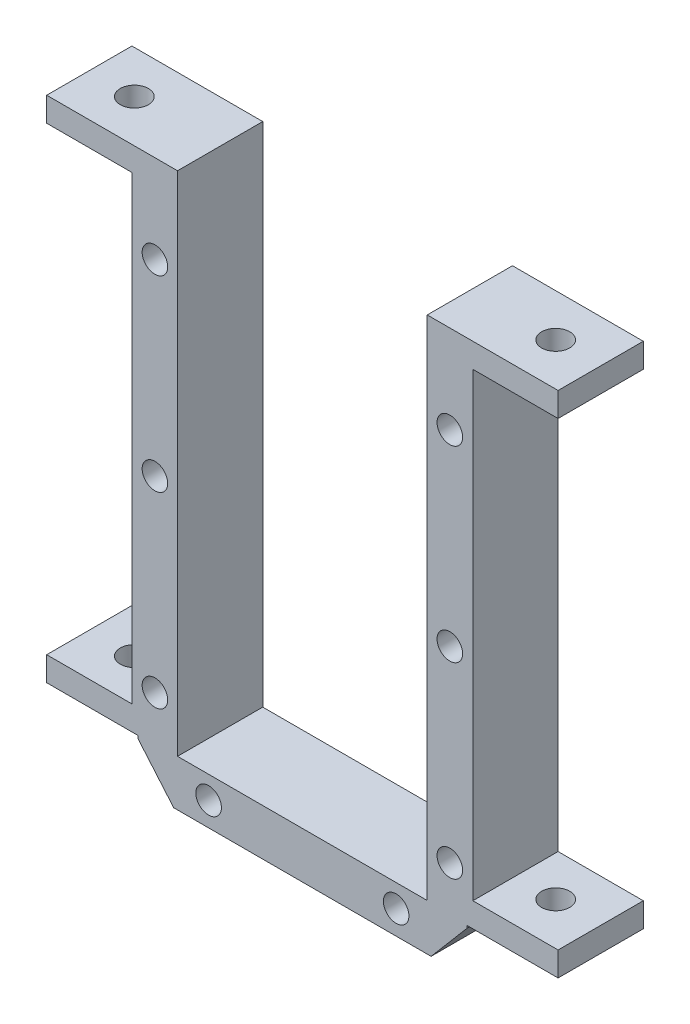
SolidWorks part; units mm, degrees
material "AISI 1035 Acier (SS)"
ref_plane "Front Plane" through (0, 0, 0) normal (0, 0, 1) x (1, 0, 0)
ref_plane "Top Plane" through (0, 0, 0) normal (0, 1, 0) x (1, 0, 0)
ref_plane "Right Plane" through (0, 0, 0) normal (1, 0, 0) x (0, 0, -1)
sketch "Sketch1" plane through (0, 0, 0) normal (0, 0, 1) x (1, 0, 0)
  line L1 (-20.1, 32.55) -> (19.9, 32.55)
  line L2 (-20.1, 32.55) -> (-20.1, -32.55)
  line L3 (-20.1, -32.55) -> (19.9, -32.55)
  line L4 (19.9, 32.55) -> (19.9, -32.55)
  point P0 (0, 0)
  dimension "D1" = 40
  dimension "D2" = 65.1
extrude "Boss-Extrude1" add sketch "Sketch1" along normal blind 10
sketch "Sketch2" plane through (0, 0, 10) normal (0, 0, 1) x (1, 0, 0)
  line L0 (-0.1, 32.55) -> (-0.1, -32.55) construction
  line L1 (19.9, 32.55) -> (-20.1, 32.55) construction
  line L2 (-20.1, -32.55) -> (19.9, -32.55) construction
  line L3 (-20.1, 0) -> (19.9, 0) construction
  line L4 (-20.1, 32.55) -> (-20.1, -32.55) construction
  line L5 (19.9, -32.55) -> (19.9, 32.55) construction
  line L6 (-20.1, -27.45) -> (19.9, -27.45) construction
  line L7 (15, -32.55) -> (19.335, -27.45)
  line L8 (19.335, -27.45) -> (15, -32.55) construction
  line L9 (19.335, -27.45) -> (19.9, -27.45)
  line L22 (19.9, -27.45) -> (19.9, -32.55)
  line L23 (19.9, -32.55) -> (15, -32.55)
  line L24 (-20.1, -27.45) -> (-20.1, -32.55)
  line L25 (-19.535, -27.45) -> (-20.1, -27.45)
  line L26 (-15.2, -32.55) -> (-19.535, -27.45)
  line L27 (-20.1, -32.55) -> (-15.2, -32.55)
  point P12 (-0.1, -27.45)
  point P13 (-19.535, -27.45)
  point P17 (-0.1, -27.45)
  point P18 (19.335, -27.45)
  dimension "D1" = 60
extrude "Cut-Extrude1" cut sketch "Sketch2" against normal blind 10
sketch "Sketch4" plane through (0, 0, 10) normal (0, 0, 1) x (1, 0, 0)
  line L0 (-0.1, 32.55) -> (-0.1, -32.55) construction
  line L1 (19.9, 32.55) -> (-20.1, 32.55) construction
  line L2 (-15.2, -32.55) -> (15, -32.55) construction
  line L3 (-20.1, 2.55) -> (19.9, 2.55) construction
  line L4 (-20.1, 32.55) -> (-20.1, -27.45) construction
  line L5 (19.9, -27.45) -> (19.9, 32.55) construction
  line L6 (14.55, -26.95) -> (-14.75, -26.95) construction
  line L7 (-14.75, -26.95) -> (-14.75, 32.55) construction
  line L8 (14.55, -26.95) -> (14.55, 32.55) construction
  line L9 (-14.75, 32.55) -> (-14.75, -26.95)
  line L10 (-14.75, -26.95) -> (14.55, -26.95)
  line L11 (14.55, -26.95) -> (14.55, 32.55)
  line L12 (14.55, 32.55) -> (-14.75, 32.55)
  point P12 (-0.1, -26.95)
  point P16 (-0.1, -26.95)
  dimension "D1" = 5.6
  dimension "D2" = 29.3
extrude "Cut-Extrude2" cut sketch "Sketch4" against normal blind 10
sketch "Sketch5" plane through (0, 0, 10) normal (0, 0, 1) x (1, 0, 0)
  line L0 (-14.75, 32.55) -> (14.55, 32.55) construction
  line L1 (-0.1, 32.55) -> (-0.1, -32.55) construction
  line L2 (-15.2, -32.55) -> (15, -32.55) construction
  line L3 (-15.2, -32.55) -> (15, -32.55) construction
  line L6 (-20.1, 32.55) -> (-20.1, -27.45) construction
  circle A0 centre (-17.4, 22.05) radius 1.5
  circle A1 centre (-17.4, 0.05) radius 1.5
  circle A2 centre (-17.4, -21.95) radius 1.5
  circle A3 centre (-11.1, -29.75) radius 1.5
  circle A4 centre (10.9, -29.75) radius 1.5
  circle A5 centre (17.2, -21.95) radius 1.5
  circle A6 centre (17.2, 0.05) radius 1.5
  circle A7 centre (17.2, 22.05) radius 1.5
  point P8 (-17.4, 22.05)
  point P9 (-17.4, 0.05)
  point P10 (-17.4, -21.95)
  point P11 (-11.1, -29.75)
  point P22 (10.9, -29.75)
  point P25 (17.2, -21.95)
  point P28 (17.2, 0.05)
  point P31 (17.2, 22.05)
  dimension "D6" = 3
  dimension "D7" = 3
  dimension "D8" = 3
  dimension "D9" = 3
  dimension "D1" = 10.6
  dimension "D2" = 32.6
  dimension "D3" = 54.6
  dimension "D4" = 2.8
  dimension "D5" = 9
  dimension "D10" = 17.3
  dimension "D11" = 17.3
  dimension "D12" = 17.3
extrude "Cut-Extrude3" cut sketch "Sketch5" against normal blind 10
sketch "Sketch6" plane through (0, 0, 10) normal (0, 0, 1) x (1, 0, 0)
  line L0 (-14.75, 32.55) -> (14.55, 32.55) construction
  line L1 (-0.1, 32.55) -> (-0.1, -32.55) construction
  line L2 (-15.2, -32.55) -> (15, -32.55) construction
  line L3 (-20.1, 2.55) -> (19.9, 2.55) construction
  line L4 (-20.1, 32.55) -> (-20.1, -27.45) construction
  line L5 (19.9, -27.45) -> (19.9, 32.55) construction
sketch "Sketch7" plane through (19.9, 0, 0) normal (1, 0, 0) x (0, 0, -1)
  line L0 (0, 2.55) -> (-10, 2.55) construction
  line L1 (-10, 32.55) -> (-10, -32.55) construction
  line L2 (0, -27.45) -> (0, 32.55) construction
  line L3 (0, 29.55) -> (-10, 29.55)
  line L4 (-10, 29.55) -> (-10, 32.55)
  line L5 (-10, 32.55) -> (0, 32.55)
  line L6 (0, 32.55) -> (0, 29.55)
  line L7 (-10, -27.45) -> (-10, 32.55) construction
  line L8 (-10, -27.45) -> (0, -27.45)
  line L9 (-10, -24.45) -> (-10, -27.45)
  line L10 (0, -24.45) -> (-10, -24.45)
  line L11 (0, -27.45) -> (0, -24.45)
  point P5 (0, 29.55)
  dimension "D1" = 3
extrude "Boss-Extrude2" add sketch "Sketch7" along normal blind 10
sketch "Sketch8" plane through (-20.1, 0, 0) normal (-1, 0, 0) x (0, 0, 1)
  line L0 (0, 2.55) -> (10, 2.55) construction
  line L1 (0, 32.55) -> (0, -27.45) construction
  line L2 (10, 32.55) -> (10, -32.55) construction
  line L3 (0, 29.55) -> (10, 29.55)
  line L4 (10, 29.55) -> (10, 32.55)
  line L5 (10, 32.55) -> (0, 32.55)
  line L6 (0, 32.55) -> (0, 29.55)
  line L7 (10, -27.45) -> (0, -27.45)
  line L8 (10, -24.45) -> (10, -27.45)
  line L9 (0, -24.45) -> (10, -24.45)
  line L10 (0, -27.45) -> (0, -24.45)
  point P6 (0, 29.55)
  dimension "D1" = 3
extrude "Boss-Extrude3" add sketch "Sketch8" along normal blind 10
sketch "Sketch9" plane through (0, -27.45, 0) normal (0, -1, 0) x (-1, 0, 0)
  line L0 (24.8175, -10) -> (24.8175, 0) construction
  line L1 (19.535, -10) -> (30.1, -10) construction
  line L2 (19.535, 0) -> (30.1, 0) construction
  line L3 (30.1, -5) -> (19.535, -5) construction
  line L4 (30.1, 0) -> (30.1, -10) construction
  line L5 (19.535, 0) -> (19.535, -10) construction
  circle A0 centre (24.8175, -5) radius 1.65
  dimension "D1" = 3.3
extrude "Cut-Extrude4" cut sketch "Sketch9" against normal through all
sketch "Sketch10" plane through (0, -27.45, 0) normal (0, -1, 0) x (-1, 0, 0)
  line L0 (-24.6175, -10) -> (-24.6175, 0) construction
  line L1 (-29.9, -10) -> (-19.335, -10) construction
  line L2 (-29.9, 0) -> (-19.335, 0) construction
  line L3 (-19.335, -5) -> (-29.9, -5) construction
  line L4 (-19.335, 0) -> (-19.335, -10) construction
  line L5 (-29.9, -10) -> (-29.9, 0) construction
  circle A0 centre (-24.6175, -5) radius 1.65
  dimension "D1" = 3.3
extrude "Cut-Extrude5" cut sketch "Sketch10" against normal through all
sketch "Esquisse1" plane through (0, 0, 10) normal (0, 0, 1) x (1, 0, 0)
  line L6 (29.9, -27.45) -> (29.9, -27.3)
  line L7 (29.9, -24.45) -> (29.9, -27.45) construction
  line L8 (29.9, -27.3) -> (19.335, -27.3)
  line L9 (19.335, -27.3) -> (19.185, -27.3)
  line L10 (29.9, 32.55) -> (29.9, 32.4)
  line L11 (19.185, -27.3) -> (19.185, -27.9056)
  line L12 (19.185, -27.9056) -> (27.185, -27.9056)
  line L14 (29.9, 32.55) -> (29.9, 29.55) construction
  line L15 (29.9, 32.4) -> (14.55, 32.4)
  line L16 (14.55, -26.95) -> (14.55, 32.55) construction
  line L17 (14.55, 32.4) -> (14.55, 32.55)
  line L18 (14.55, 32.55) -> (29.9, 32.55)
  line L31 (27.185, -27.9056) -> (27.185, -27.45)
  line L32 (29.9, -27.45) -> (19.335, -27.45) construction
  line L33 (27.185, -27.45) -> (29.9, -27.45)
  line L34 (-15.2, -32.55) -> (15, -32.55) construction
  line L35 (-0.1, -32.55) -> (-0.1, -23.8847) construction
  line L36 (-27.385, -27.9056) -> (-27.385, -27.45)
  line L37 (-19.385, -27.9056) -> (-27.385, -27.9056)
  line L38 (-19.385, -27.3) -> (-19.385, -27.9056)
  line L39 (-19.535, -27.3) -> (-19.385, -27.3)
  line L40 (-30.1, -27.3) -> (-19.535, -27.3)
  line L41 (-30.1, -27.45) -> (-30.1, -27.3)
  line L42 (-27.385, -27.45) -> (-30.1, -27.45)
  line L43 (-14.75, 32.4) -> (-14.75, 32.55)
  line L44 (-30.1, 32.4) -> (-14.75, 32.4)
  line L45 (-30.1, 32.55) -> (-30.1, 32.4)
  line L46 (-14.75, 32.55) -> (-30.1, 32.55)
  line L47 (-14.75, -26.95) -> (14.55, -26.95)
  line L48 (-14.75, -26.95) -> (-14.75, -27.1)
  line L49 (-14.75, -27.1) -> (14.55, -27.1)
  line L50 (14.55, -26.95) -> (14.55, -27.1)
  dimension "D1" = 0.15
  dimension "D2" = 0.15
  dimension "D3" = 0.6056
  dimension "D4" = 8
  dimension "D5" = 0.15
  dimension "D6" = 2.715
  dimension "D7" = 15.1
  dimension "D8" = 0.15
extrude "Enlèv. mat.-Extru.1" cut sketch "Esquisse1" against normal through all
